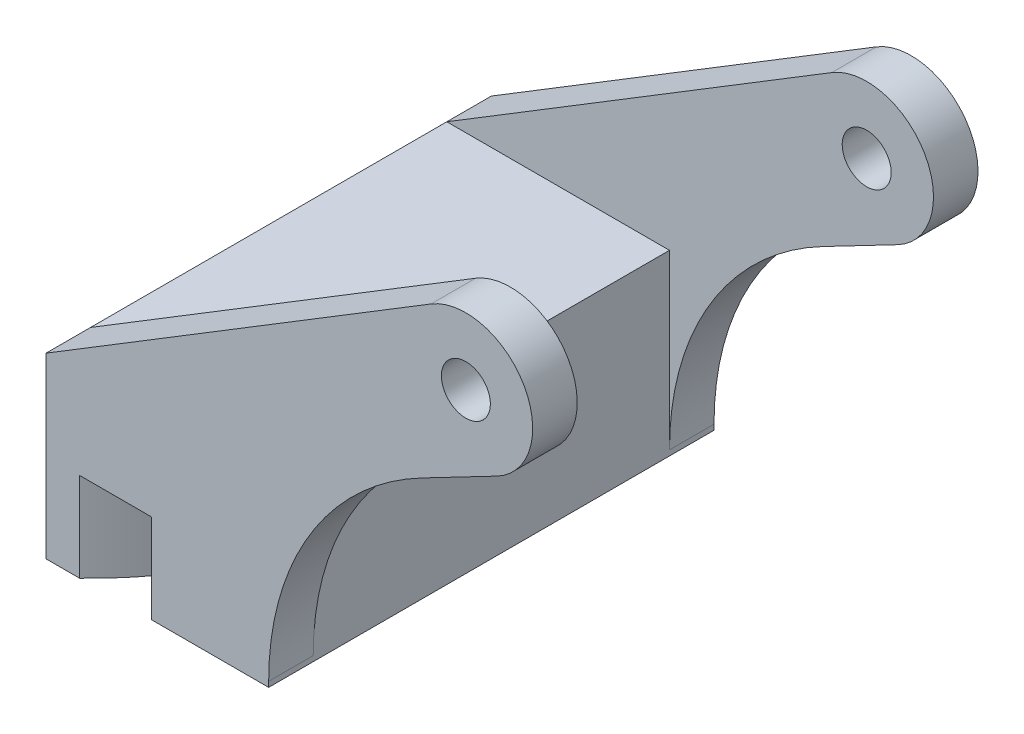
SolidWorks part; units mm, degrees
ref_plane "Front Plane" through (0, 0, 0) normal (0, 0, 1) x (1, 0, 0)
ref_plane "Top Plane" through (0, 0, 0) normal (0, 1, 0) x (1, 0, 0)
ref_plane "Right Plane" through (0, 0, 0) normal (1, 0, 0) x (0, 0, -1)
sketch "Sketch1" plane through (0, 0, 0) normal (0, 0, 1) x (1, 0, 0)
  line L0 (0, 0) -> (-43.9941, -25.4) construction
  line L1 (-59.8691, -25.4) -> (-28.1191, -25.4) construction
  line L2 (-59.8691, -25.4) -> (-4.9642, 8.1291)
  line L3 (4.403, -8.4462) -> (-28.1191, -25.4)
  line L4 (-59.8691, -25.4) -> (-59.8691, -38.1)
  line L5 (-59.8691, -38.1) -> (-28.1191, -38.1)
  line L6 (-28.1191, -38.1) -> (-28.1191, -25.4)
  line L7 (0, 0) -> (4.403, -8.4462) construction
  circle A0 centre (0, 0) radius 3.4925
  arc A1 (4.403, -8.4462) -> (-4.9642, 8.1291) centre (0, 0) ccw
  dimension "D2" = 6.985
  dimension "D4" = 19.05
  dimension "D1" = 30
  dimension "D3" = 31.75
  dimension "D5" = 12.7
  dimension "D6" = 50.8
  dimension "D7" = 90
extrude "Boss-Extrude1" add sketch "Sketch1" along normal blind 63.5
sketch "Sketch2" plane through (0, 0, 0) normal (1, 0, 0) x (0, 0, -1)
  line L1 (-57.15, -25.4) -> (-6.35, -25.4)
  line L2 (-57.15, -25.4) -> (-57.15, 9.525)
  line L3 (-57.15, 9.525) -> (-6.35, 9.525)
  line L4 (-6.35, -25.4) -> (-6.35, 9.525)
  line L5 (0, 9.525) -> (-63.5, 9.525) construction
  line L8 (-63.5, -38.1) -> (-63.5, -25.4) construction
  line L9 (0, -38.1) -> (0, -25.4) construction
  line L11 (-63.5, -25.4) -> (0, -25.4) construction
  dimension "D1" = 6.35
  dimension "D2" = 6.35
extrude "Cut-Extrude1" cut sketch "Sketch2" against normal through all both and the other way through all
sketch "Sketch3" plane through (0, -38.1, 0) normal (0, -1, 0) x (1, 0, 0)
  line L0 (-59.8691, 31.75) -> (-85.2691, 31.75) construction
  line L2 (-33.8341, 63.5) -> (-33.8341, 0) construction
  line L3 (-59.8691, 63.5) -> (-28.1191, 63.5) construction
  line L4 (-59.8691, 0) -> (-28.1191, 0) construction
  line L5 (-55.0749, 63.5) -> (-55.0749, 0) construction
  line L6 (-55.0749, 63.5) -> (-59.8691, 63.5)
  line L7 (-59.8691, 63.5) -> (-59.8691, 0)
  line L8 (-59.8691, 0) -> (-55.0749, 0)
  line L9 (-44.8031, 63.5) -> (-28.1191, 63.5)
  line L10 (-28.1191, 63.5) -> (-28.1191, 0)
  line L11 (-28.1191, 0) -> (-44.8031, 0)
  arc A0 (-44.8031, 0) -> (-44.8031, 63.5) centre (-85.2691, 31.75) ccw
  arc A1 (-55.0749, 0) -> (-55.0749, 63.5) centre (-85.2691, 31.75) ccw
  dimension "D1" = 102.87
  dimension "D2" = 87.63
  dimension "D3" = 21.2408
  dimension "D4" = 25.4
extrude "Boss-Extrude2" add sketch "Sketch3" along normal blind 12.7
fillet "Fillet2" radius 40.64 2 edges at (-28.1191, -25.4, 3.175) (-28.1191, -25.4, 60.325)
